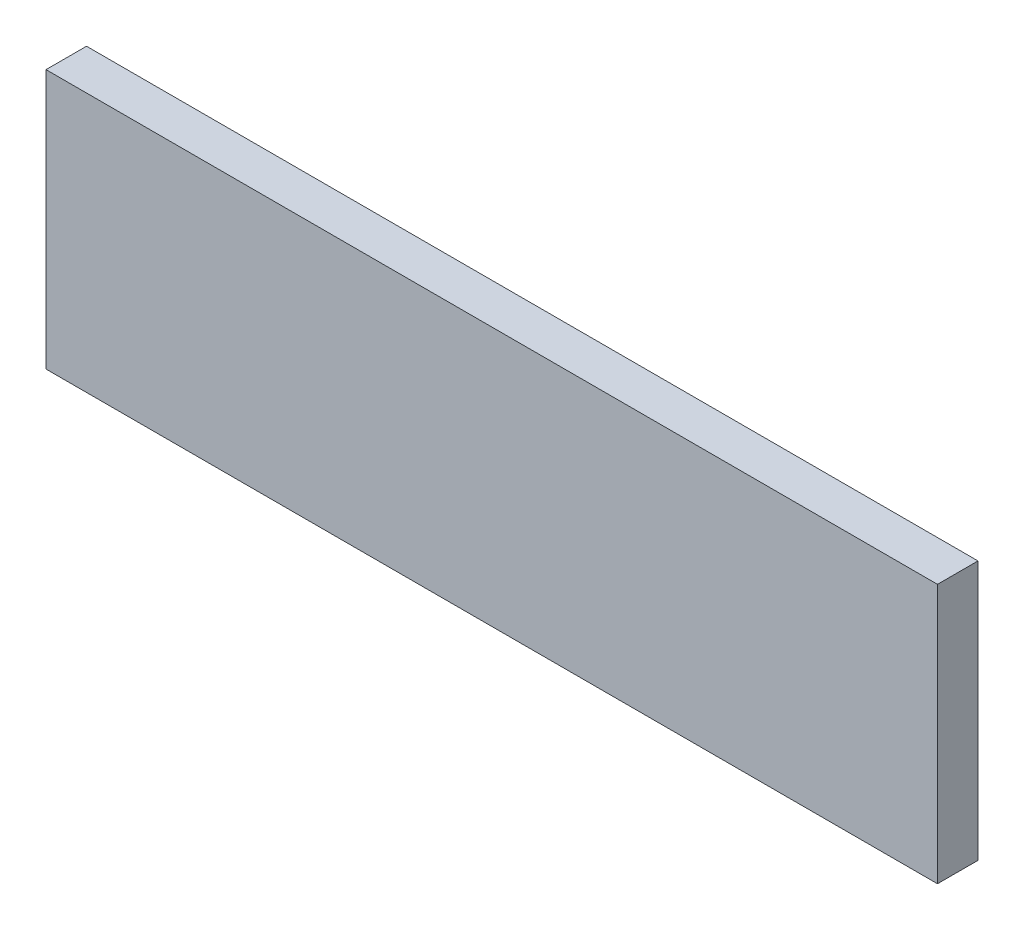
SolidWorks part; units mm, degrees
ref_plane "Front Plane" through (0, 0, 0) normal (0, 0, 1) x (1, 0, 0)
ref_plane "Top Plane" through (0, 0, 0) normal (0, 1, 0) x (1, 0, 0)
ref_plane "Right Plane" through (0, 0, 0) normal (1, 0, 0) x (0, 0, -1)
sketch "Sketch1" plane through (0, 0, 0) normal (0, 0, 1) x (1, 0, 0)
  line L1 (-27.5, -8) -> (27.5, -8)
  line L2 (-27.5, -8) -> (-27.5, 8)
  line L3 (-27.5, 8) -> (27.5, 8)
  line L4 (27.5, -8) -> (27.5, 8)
  line L5 (-27.5, -8) -> (27.5, 8) construction
  line L6 (-27.5, 8) -> (27.5, -8) construction
  point P0 (0, 0)
  dimension "D1" = 55
  dimension "D2" = 16
extrude "Boss-Extrude1" add sketch "Sketch1" along normal blind 2.5
